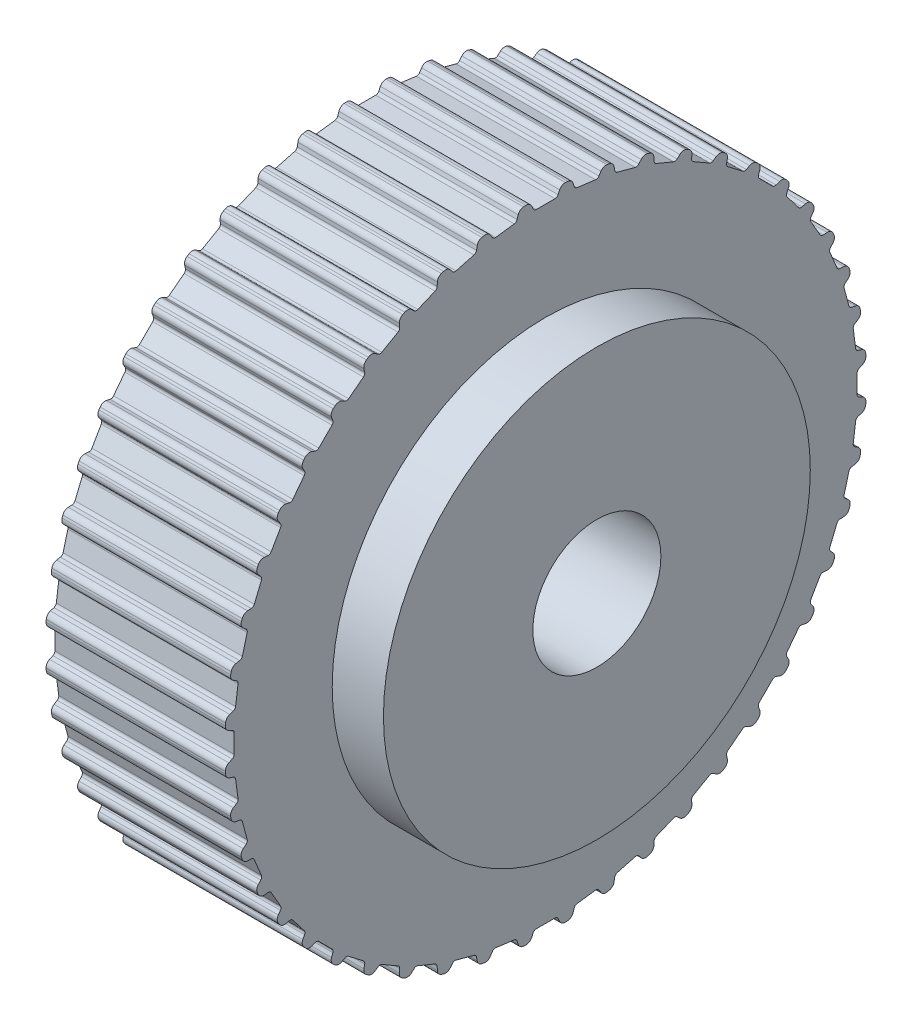
SolidWorks part; units mm, degrees
ref_plane "Front Plane" through (0, 0, 0) normal (0, 0, 1) x (1, 0, 0)
ref_plane "Top Plane" through (0, 0, 0) normal (0, 1, 0) x (1, 0, 0)
ref_plane "Right Plane" through (0, 0, 0) normal (1, 0, 0) x (0, 0, -1)
ref_plane "Plane1" through (0, 0, 0) normal (0, 0, -1) x (-1, 0, 0)
sketch "Sketch1" plane through (0, 0, 0) normal (0, 0, -1) x (-1, 0, 0)
  line L0 (-21, 37.585) -> (-21, 0)
  line L1 (-21, 0) -> (0, 0)
  line L2 (0, 0) -> (0, 37.585)
  line L3 (0, 37.585) -> (-21, 37.585)
  line L4 (-21, 0) -> (0, 0) construction
revolve "Revolve1" add sketch "Sketch1" angle 360 about L4
sketch "Sketch2" plane through (0, 0, 0) normal (-1, 0, 0) x (0, 0, 1)
  line L0 (3.0738, 37.4591) -> (3.4238, 36.3491)
  line L1 (3.4238, 36.3491) -> (6.1007, 35.9967)
  line L2 (6.1007, 35.9967) -> (6.7261, 36.9783)
  arc A0 (6.7261, 36.9783) -> (3.0738, 37.4591) centre (0, 0) ccw
extrude "Cut-Extrude1" cut sketch "Sketch2" against normal through all
sketch "Sketch3" plane through (0, 0, 0) normal (-1, 0, 0) x (0, 0, 1)
  line L0 (7.9369, 36.7374) -> (8.139, 35.5912)
  line L1 (8.139, 35.5912) -> (10.747, 34.8924)
  line L2 (10.747, 34.8924) -> (11.4951, 35.784)
  arc A0 (11.4951, 35.784) -> (7.9369, 36.7374) centre (0, 0) ccw
extrude "Cut-Extrude2" cut sketch "Sketch3" against normal through all
sketch "Sketch4" plane through (0, 0, 0) normal (-1, 0, 0) x (0, 0, 1)
  line L0 (12.6642, 35.3871) -> (12.715, 34.2244)
  line L1 (12.715, 34.2244) -> (15.2094, 33.1911)
  line L2 (15.2094, 33.1911) -> (16.0676, 33.9774)
  arc A0 (16.0676, 33.9774) -> (12.6642, 35.3871) centre (0, 0) ccw
extrude "Cut-Extrude3" cut sketch "Sketch4" against normal through all
sketch "Sketch5" plane through (0, 0, 0) normal (-1, 0, 0) x (0, 0, 1)
  line L0 (17.1748, 33.4314) -> (17.0734, 32.2719)
  line L1 (17.0734, 32.2719) -> (19.4116, 30.9219)
  line L2 (19.4116, 30.9219) -> (20.365, 31.5895)
  arc A0 (20.365, 31.5895) -> (17.1748, 33.4314) centre (0, 0) ccw
extrude "Cut-Extrude4" cut sketch "Sketch5" against normal through all
sketch "Sketch6" plane through (0, 0, 0) normal (-1, 0, 0) x (0, 0, 1)
  line L0 (21.3915, 30.9036) -> (21.1396, 29.7673)
  line L1 (21.1396, 29.7673) -> (23.2817, 28.1237)
  line L2 (23.2817, 28.1237) -> (24.3141, 28.6611)
  arc A0 (24.3141, 28.6611) -> (21.3915, 30.9036) centre (0, 0) ccw
extrude "Cut-Extrude5" cut sketch "Sketch6" against normal through all
sketch "Sketch7" plane through (0, 0, 0) normal (-1, 0, 0) x (0, 0, 1)
  line L0 (25.2423, 27.8471) -> (24.8442, 26.7534)
  line L1 (24.8442, 26.7534) -> (26.7534, 24.8442)
  line L2 (26.7534, 24.8442) -> (27.8471, 25.2423)
  arc A0 (27.8471, 25.2423) -> (25.2423, 27.8471) centre (0, 0) ccw
extrude "Cut-Extrude6" cut sketch "Sketch7" against normal through all
sketch "Sketch8" plane through (0, 0, 0) normal (-1, 0, 0) x (0, 0, 1)
  line L0 (28.6611, 24.3141) -> (28.1237, 23.2817)
  line L1 (28.1237, 23.2817) -> (29.7673, 21.1396)
  line L2 (29.7673, 21.1396) -> (30.9036, 21.3915)
  arc A0 (30.9036, 21.3915) -> (28.6611, 24.3141) centre (0, 0) ccw
extrude "Cut-Extrude7" cut sketch "Sketch8" against normal through all
sketch "Sketch9" plane through (0, 0, 0) normal (-1, 0, 0) x (0, 0, 1)
  line L0 (31.5895, 20.365) -> (30.9219, 19.4116)
  line L1 (30.9219, 19.4116) -> (32.2719, 17.0734)
  line L2 (32.2719, 17.0734) -> (33.4314, 17.1748)
  arc A0 (33.4314, 17.1748) -> (31.5895, 20.365) centre (0, 0) ccw
extrude "Cut-Extrude8" cut sketch "Sketch9" against normal through all
sketch "Sketch10" plane through (0, 0, 0) normal (-1, 0, 0) x (0, 0, 1)
  line L0 (33.9774, 16.0676) -> (33.1911, 15.2094)
  line L1 (33.1911, 15.2094) -> (34.2244, 12.715)
  line L2 (34.2244, 12.715) -> (35.3871, 12.6642)
  arc A0 (35.3871, 12.6642) -> (33.9774, 16.0676) centre (0, 0) ccw
extrude "Cut-Extrude9" cut sketch "Sketch10" against normal through all
sketch "Sketch11" plane through (0, 0, 0) normal (-1, 0, 0) x (0, 0, 1)
  line L0 (35.784, 11.4951) -> (34.8924, 10.747)
  line L1 (34.8924, 10.747) -> (35.5912, 8.139)
  line L2 (35.5912, 8.139) -> (36.7374, 7.9369)
  arc A0 (36.7374, 7.9369) -> (35.784, 11.4951) centre (0, 0) ccw
extrude "Cut-Extrude10" cut sketch "Sketch11" against normal through all
sketch "Sketch12" plane through (0, 0, 0) normal (-1, 0, 0) x (0, 0, 1)
  line L0 (36.9783, 6.7261) -> (35.9967, 6.1007)
  line L1 (35.9967, 6.1007) -> (36.3491, 3.4238)
  line L2 (36.3491, 3.4238) -> (37.4591, 3.0738)
  arc A0 (37.4591, 3.0738) -> (36.9783, 6.7261) centre (0, 0) ccw
extrude "Cut-Extrude11" cut sketch "Sketch12" against normal through all
sketch "Sketch13" plane through (0, 0, 0) normal (-1, 0, 0) x (0, 0, 1)
  line L0 (37.5398, 1.8419) -> (36.485, 1.35)
  line L1 (36.485, 1.35) -> (36.485, -1.35)
  line L2 (36.485, -1.35) -> (37.5398, -1.8419)
  arc A0 (37.5398, -1.8419) -> (37.5398, 1.8419) centre (0, 0) ccw
extrude "Cut-Extrude12" cut sketch "Sketch13" against normal through all
sketch "Sketch14" plane through (0, 0, 0) normal (-1, 0, 0) x (0, 0, 1)
  line L0 (37.4591, -3.0738) -> (36.3491, -3.4238)
  line L1 (36.3491, -3.4238) -> (35.9967, -6.1007)
  line L2 (35.9967, -6.1007) -> (36.9783, -6.7261)
  arc A0 (36.9783, -6.7261) -> (37.4591, -3.0738) centre (0, 0) ccw
extrude "Cut-Extrude13" cut sketch "Sketch14" against normal through all
sketch "Sketch15" plane through (0, 0, 0) normal (-1, 0, 0) x (0, 0, 1)
  line L0 (36.7374, -7.9369) -> (35.5912, -8.139)
  line L1 (35.5912, -8.139) -> (34.8924, -10.747)
  line L2 (34.8924, -10.747) -> (35.784, -11.4951)
  arc A0 (35.784, -11.4951) -> (36.7374, -7.9369) centre (0, 0) ccw
extrude "Cut-Extrude14" cut sketch "Sketch15" against normal through all
sketch "Sketch16" plane through (0, 0, 0) normal (-1, 0, 0) x (0, 0, 1)
  line L0 (35.3871, -12.6642) -> (34.2244, -12.715)
  line L1 (34.2244, -12.715) -> (33.1911, -15.2094)
  line L2 (33.1911, -15.2094) -> (33.9774, -16.0676)
  arc A0 (33.9774, -16.0676) -> (35.3871, -12.6642) centre (0, 0) ccw
extrude "Cut-Extrude15" cut sketch "Sketch16" against normal through all
sketch "Sketch17" plane through (0, 0, 0) normal (-1, 0, 0) x (0, 0, 1)
  line L0 (33.4314, -17.1748) -> (32.2719, -17.0734)
  line L1 (32.2719, -17.0734) -> (30.9219, -19.4116)
  line L2 (30.9219, -19.4116) -> (31.5895, -20.365)
  arc A0 (31.5895, -20.365) -> (33.4314, -17.1748) centre (0, 0) ccw
extrude "Cut-Extrude16" cut sketch "Sketch17" against normal through all
sketch "Sketch18" plane through (0, 0, 0) normal (-1, 0, 0) x (0, 0, 1)
  line L0 (30.9036, -21.3915) -> (29.7673, -21.1396)
  line L1 (29.7673, -21.1396) -> (28.1237, -23.2817)
  line L2 (28.1237, -23.2817) -> (28.6611, -24.3141)
  arc A0 (28.6611, -24.3141) -> (30.9036, -21.3915) centre (0, 0) ccw
extrude "Cut-Extrude17" cut sketch "Sketch18" against normal through all
sketch "Sketch19" plane through (0, 0, 0) normal (-1, 0, 0) x (0, 0, 1)
  line L0 (27.8471, -25.2423) -> (26.7534, -24.8442)
  line L1 (26.7534, -24.8442) -> (24.8442, -26.7534)
  line L2 (24.8442, -26.7534) -> (25.2423, -27.8471)
  arc A0 (25.2423, -27.8471) -> (27.8471, -25.2423) centre (0, 0) ccw
extrude "Cut-Extrude18" cut sketch "Sketch19" against normal through all
sketch "Sketch20" plane through (0, 0, 0) normal (-1, 0, 0) x (0, 0, 1)
  line L0 (24.3141, -28.6611) -> (23.2817, -28.1237)
  line L1 (23.2817, -28.1237) -> (21.1396, -29.7673)
  line L2 (21.1396, -29.7673) -> (21.3915, -30.9036)
  arc A0 (21.3915, -30.9036) -> (24.3141, -28.6611) centre (0, 0) ccw
extrude "Cut-Extrude19" cut sketch "Sketch20" against normal through all
sketch "Sketch21" plane through (0, 0, 0) normal (-1, 0, 0) x (0, 0, 1)
  line L0 (20.365, -31.5895) -> (19.4116, -30.9219)
  line L1 (19.4116, -30.9219) -> (17.0734, -32.2719)
  line L2 (17.0734, -32.2719) -> (17.1748, -33.4314)
  arc A0 (17.1748, -33.4314) -> (20.365, -31.5895) centre (0, 0) ccw
extrude "Cut-Extrude20" cut sketch "Sketch21" against normal through all
sketch "Sketch22" plane through (0, 0, 0) normal (-1, 0, 0) x (0, 0, 1)
  line L0 (16.0676, -33.9774) -> (15.2094, -33.1911)
  line L1 (15.2094, -33.1911) -> (12.715, -34.2244)
  line L2 (12.715, -34.2244) -> (12.6642, -35.3871)
  arc A0 (12.6642, -35.3871) -> (16.0676, -33.9774) centre (0, 0) ccw
extrude "Cut-Extrude21" cut sketch "Sketch22" against normal through all
sketch "Sketch23" plane through (0, 0, 0) normal (-1, 0, 0) x (0, 0, 1)
  line L0 (11.4951, -35.784) -> (10.747, -34.8924)
  line L1 (10.747, -34.8924) -> (8.139, -35.5912)
  line L2 (8.139, -35.5912) -> (7.9369, -36.7374)
  arc A0 (7.9369, -36.7374) -> (11.4951, -35.784) centre (0, 0) ccw
extrude "Cut-Extrude22" cut sketch "Sketch23" against normal through all
sketch "Sketch24" plane through (0, 0, 0) normal (-1, 0, 0) x (0, 0, 1)
  line L0 (6.7261, -36.9783) -> (6.1007, -35.9967)
  line L1 (6.1007, -35.9967) -> (3.4238, -36.3491)
  line L2 (3.4238, -36.3491) -> (3.0738, -37.4591)
  arc A0 (3.0738, -37.4591) -> (6.7261, -36.9783) centre (0, 0) ccw
extrude "Cut-Extrude23" cut sketch "Sketch24" against normal through all
sketch "Sketch25" plane through (0, 0, 0) normal (-1, 0, 0) x (0, 0, 1)
  line L0 (1.8419, -37.5398) -> (1.35, -36.485)
  line L1 (1.35, -36.485) -> (-1.35, -36.485)
  line L2 (-1.35, -36.485) -> (-1.8419, -37.5398)
  arc A0 (-1.8419, -37.5398) -> (1.8419, -37.5398) centre (0, 0) ccw
extrude "Cut-Extrude24" cut sketch "Sketch25" against normal through all
sketch "Sketch26" plane through (0, 0, 0) normal (-1, 0, 0) x (0, 0, 1)
  line L0 (-3.0738, -37.4591) -> (-3.4238, -36.3491)
  line L1 (-3.4238, -36.3491) -> (-6.1007, -35.9967)
  line L2 (-6.1007, -35.9967) -> (-6.7261, -36.9783)
  arc A0 (-6.7261, -36.9783) -> (-3.0738, -37.4591) centre (0, 0) ccw
extrude "Cut-Extrude25" cut sketch "Sketch26" against normal through all
sketch "Sketch27" plane through (0, 0, 0) normal (-1, 0, 0) x (0, 0, 1)
  line L0 (-7.9369, -36.7374) -> (-8.139, -35.5912)
  line L1 (-8.139, -35.5912) -> (-10.747, -34.8924)
  line L2 (-10.747, -34.8924) -> (-11.4951, -35.784)
  arc A0 (-11.4951, -35.784) -> (-7.9369, -36.7374) centre (0, 0) ccw
extrude "Cut-Extrude26" cut sketch "Sketch27" against normal through all
sketch "Sketch28" plane through (0, 0, 0) normal (-1, 0, 0) x (0, 0, 1)
  line L0 (-12.6642, -35.3871) -> (-12.715, -34.2244)
  line L1 (-12.715, -34.2244) -> (-15.2094, -33.1911)
  line L2 (-15.2094, -33.1911) -> (-16.0676, -33.9774)
  arc A0 (-16.0676, -33.9774) -> (-12.6642, -35.3871) centre (0, 0) ccw
extrude "Cut-Extrude27" cut sketch "Sketch28" against normal through all
sketch "Sketch29" plane through (0, 0, 0) normal (-1, 0, 0) x (0, 0, 1)
  line L0 (-17.1748, -33.4314) -> (-17.0734, -32.2719)
  line L1 (-17.0734, -32.2719) -> (-19.4116, -30.9219)
  line L2 (-19.4116, -30.9219) -> (-20.365, -31.5895)
  arc A0 (-20.365, -31.5895) -> (-17.1748, -33.4314) centre (0, 0) ccw
extrude "Cut-Extrude28" cut sketch "Sketch29" against normal through all
sketch "Sketch30" plane through (0, 0, 0) normal (-1, 0, 0) x (0, 0, 1)
  line L0 (-21.3915, -30.9036) -> (-21.1396, -29.7673)
  line L1 (-21.1396, -29.7673) -> (-23.2817, -28.1237)
  line L2 (-23.2817, -28.1237) -> (-24.3141, -28.6611)
  arc A0 (-24.3141, -28.6611) -> (-21.3915, -30.9036) centre (0, 0) ccw
extrude "Cut-Extrude29" cut sketch "Sketch30" against normal through all
sketch "Sketch31" plane through (0, 0, 0) normal (-1, 0, 0) x (0, 0, 1)
  line L0 (-25.2423, -27.8471) -> (-24.8442, -26.7534)
  line L1 (-24.8442, -26.7534) -> (-26.7534, -24.8442)
  line L2 (-26.7534, -24.8442) -> (-27.8471, -25.2423)
  arc A0 (-27.8471, -25.2423) -> (-25.2423, -27.8471) centre (0, 0) ccw
extrude "Cut-Extrude30" cut sketch "Sketch31" against normal through all
sketch "Sketch32" plane through (0, 0, 0) normal (-1, 0, 0) x (0, 0, 1)
  line L0 (-28.6611, -24.3141) -> (-28.1237, -23.2817)
  line L1 (-28.1237, -23.2817) -> (-29.7673, -21.1396)
  line L2 (-29.7673, -21.1396) -> (-30.9036, -21.3915)
  arc A0 (-30.9036, -21.3915) -> (-28.6611, -24.3141) centre (0, 0) ccw
extrude "Cut-Extrude31" cut sketch "Sketch32" against normal through all
sketch "Sketch33" plane through (0, 0, 0) normal (-1, 0, 0) x (0, 0, 1)
  line L0 (-31.5895, -20.365) -> (-30.9219, -19.4116)
  line L1 (-30.9219, -19.4116) -> (-32.2719, -17.0734)
  line L2 (-32.2719, -17.0734) -> (-33.4314, -17.1748)
  arc A0 (-33.4314, -17.1748) -> (-31.5895, -20.365) centre (0, 0) ccw
extrude "Cut-Extrude32" cut sketch "Sketch33" against normal through all
sketch "Sketch34" plane through (0, 0, 0) normal (-1, 0, 0) x (0, 0, 1)
  line L0 (-33.9774, -16.0676) -> (-33.1911, -15.2094)
  line L1 (-33.1911, -15.2094) -> (-34.2244, -12.715)
  line L2 (-34.2244, -12.715) -> (-35.3871, -12.6642)
  arc A0 (-35.3871, -12.6642) -> (-33.9774, -16.0676) centre (0, 0) ccw
extrude "Cut-Extrude33" cut sketch "Sketch34" against normal through all
sketch "Sketch35" plane through (0, 0, 0) normal (-1, 0, 0) x (0, 0, 1)
  line L0 (-35.784, -11.4951) -> (-34.8924, -10.747)
  line L1 (-34.8924, -10.747) -> (-35.5912, -8.139)
  line L2 (-35.5912, -8.139) -> (-36.7374, -7.9369)
  arc A0 (-36.7374, -7.9369) -> (-35.784, -11.4951) centre (0, 0) ccw
extrude "Cut-Extrude34" cut sketch "Sketch35" against normal through all
sketch "Sketch36" plane through (0, 0, 0) normal (-1, 0, 0) x (0, 0, 1)
  line L0 (-36.9783, -6.7261) -> (-35.9967, -6.1007)
  line L1 (-35.9967, -6.1007) -> (-36.3491, -3.4238)
  line L2 (-36.3491, -3.4238) -> (-37.4591, -3.0738)
  arc A0 (-37.4591, -3.0738) -> (-36.9783, -6.7261) centre (0, 0) ccw
extrude "Cut-Extrude35" cut sketch "Sketch36" against normal through all
sketch "Sketch37" plane through (0, 0, 0) normal (-1, 0, 0) x (0, 0, 1)
  line L0 (-37.5398, -1.8419) -> (-36.485, -1.35)
  line L1 (-36.485, -1.35) -> (-36.485, 1.35)
  line L2 (-36.485, 1.35) -> (-37.5398, 1.8419)
  arc A0 (-37.5398, 1.8419) -> (-37.5398, -1.8419) centre (0, 0) ccw
extrude "Cut-Extrude36" cut sketch "Sketch37" against normal through all
sketch "Sketch38" plane through (0, 0, 0) normal (-1, 0, 0) x (0, 0, 1)
  line L0 (-37.4591, 3.0738) -> (-36.3491, 3.4238)
  line L1 (-36.3491, 3.4238) -> (-35.9967, 6.1007)
  line L2 (-35.9967, 6.1007) -> (-36.9783, 6.7261)
  arc A0 (-36.9783, 6.7261) -> (-37.4591, 3.0738) centre (0, 0) ccw
extrude "Cut-Extrude37" cut sketch "Sketch38" against normal through all
sketch "Sketch39" plane through (0, 0, 0) normal (-1, 0, 0) x (0, 0, 1)
  line L0 (-36.7374, 7.9369) -> (-35.5912, 8.139)
  line L1 (-35.5912, 8.139) -> (-34.8924, 10.747)
  line L2 (-34.8924, 10.747) -> (-35.784, 11.4951)
  arc A0 (-35.784, 11.4951) -> (-36.7374, 7.9369) centre (0, 0) ccw
extrude "Cut-Extrude38" cut sketch "Sketch39" against normal through all
sketch "Sketch40" plane through (0, 0, 0) normal (-1, 0, 0) x (0, 0, 1)
  line L0 (-35.3871, 12.6642) -> (-34.2244, 12.715)
  line L1 (-34.2244, 12.715) -> (-33.1911, 15.2094)
  line L2 (-33.1911, 15.2094) -> (-33.9774, 16.0676)
  arc A0 (-33.9774, 16.0676) -> (-35.3871, 12.6642) centre (0, 0) ccw
extrude "Cut-Extrude39" cut sketch "Sketch40" against normal through all
sketch "Sketch41" plane through (0, 0, 0) normal (-1, 0, 0) x (0, 0, 1)
  line L0 (-33.4314, 17.1748) -> (-32.2719, 17.0734)
  line L1 (-32.2719, 17.0734) -> (-30.9219, 19.4116)
  line L2 (-30.9219, 19.4116) -> (-31.5895, 20.365)
  arc A0 (-31.5895, 20.365) -> (-33.4314, 17.1748) centre (0, 0) ccw
extrude "Cut-Extrude40" cut sketch "Sketch41" against normal through all
sketch "Sketch42" plane through (0, 0, 0) normal (-1, 0, 0) x (0, 0, 1)
  line L0 (-30.9036, 21.3915) -> (-29.7673, 21.1396)
  line L1 (-29.7673, 21.1396) -> (-28.1237, 23.2817)
  line L2 (-28.1237, 23.2817) -> (-28.6611, 24.3141)
  arc A0 (-28.6611, 24.3141) -> (-30.9036, 21.3915) centre (0, 0) ccw
extrude "Cut-Extrude41" cut sketch "Sketch42" against normal through all
sketch "Sketch43" plane through (0, 0, 0) normal (-1, 0, 0) x (0, 0, 1)
  line L0 (-27.8471, 25.2423) -> (-26.7534, 24.8442)
  line L1 (-26.7534, 24.8442) -> (-24.8442, 26.7534)
  line L2 (-24.8442, 26.7534) -> (-25.2423, 27.8471)
  arc A0 (-25.2423, 27.8471) -> (-27.8471, 25.2423) centre (0, 0) ccw
extrude "Cut-Extrude42" cut sketch "Sketch43" against normal through all
sketch "Sketch44" plane through (0, 0, 0) normal (-1, 0, 0) x (0, 0, 1)
  line L0 (-24.3141, 28.6611) -> (-23.2817, 28.1237)
  line L1 (-23.2817, 28.1237) -> (-21.1396, 29.7673)
  line L2 (-21.1396, 29.7673) -> (-21.3915, 30.9036)
  arc A0 (-21.3915, 30.9036) -> (-24.3141, 28.6611) centre (0, 0) ccw
extrude "Cut-Extrude43" cut sketch "Sketch44" against normal through all
sketch "Sketch45" plane through (0, 0, 0) normal (-1, 0, 0) x (0, 0, 1)
  line L0 (-20.365, 31.5895) -> (-19.4116, 30.9219)
  line L1 (-19.4116, 30.9219) -> (-17.0734, 32.2719)
  line L2 (-17.0734, 32.2719) -> (-17.1748, 33.4314)
  arc A0 (-17.1748, 33.4314) -> (-20.365, 31.5895) centre (0, 0) ccw
extrude "Cut-Extrude44" cut sketch "Sketch45" against normal through all
sketch "Sketch46" plane through (0, 0, 0) normal (-1, 0, 0) x (0, 0, 1)
  line L0 (-16.0676, 33.9774) -> (-15.2094, 33.1911)
  line L1 (-15.2094, 33.1911) -> (-12.715, 34.2244)
  line L2 (-12.715, 34.2244) -> (-12.6642, 35.3871)
  arc A0 (-12.6642, 35.3871) -> (-16.0676, 33.9774) centre (0, 0) ccw
extrude "Cut-Extrude45" cut sketch "Sketch46" against normal through all
sketch "Sketch47" plane through (0, 0, 0) normal (-1, 0, 0) x (0, 0, 1)
  line L0 (-11.4951, 35.784) -> (-10.747, 34.8924)
  line L1 (-10.747, 34.8924) -> (-8.139, 35.5912)
  line L2 (-8.139, 35.5912) -> (-7.9369, 36.7374)
  arc A0 (-7.9369, 36.7374) -> (-11.4951, 35.784) centre (0, 0) ccw
extrude "Cut-Extrude46" cut sketch "Sketch47" against normal through all
sketch "Sketch48" plane through (0, 0, 0) normal (-1, 0, 0) x (0, 0, 1)
  line L0 (-6.7261, 36.9783) -> (-6.1007, 35.9967)
  line L1 (-6.1007, 35.9967) -> (-3.4238, 36.3491)
  line L2 (-3.4238, 36.3491) -> (-3.0738, 37.4591)
  arc A0 (-3.0738, 37.4591) -> (-6.7261, 36.9783) centre (0, 0) ccw
extrude "Cut-Extrude47" cut sketch "Sketch48" against normal through all
sketch "Sketch49" plane through (0, 0, 0) normal (-1, 0, 0) x (0, 0, 1)
  line L0 (-1.8419, 37.5398) -> (-1.35, 36.485)
  line L1 (-1.35, 36.485) -> (1.35, 36.485)
  line L2 (1.35, 36.485) -> (1.8419, 37.5398)
  arc A0 (1.8419, 37.5398) -> (-1.8419, 37.5398) centre (0, 0) ccw
extrude "Cut-Extrude48" cut sketch "Sketch49" against normal through all
sketch "Sketch50" plane through (0, 0, 0) normal (0, 0, -1) x (-1, 0, 0)
  line L0 (-27, 25) -> (-27, 0)
  line L1 (-27, 0) -> (-21, 0)
  line L2 (-21, 0) -> (-21, 25)
  line L3 (-21, 25) -> (-27, 25)
  line L4 (-27, 0) -> (-21, 0) construction
revolve "Revolve2" add sketch "Sketch50" angle 360 about L4
hole_wizard "Ø8.0 (8) Diameter Hole1" positions "Sketch52" profile "Sketch51" hole size "Ø8.0" standard "ANSI Metric"
sketch "Sketch52" plane through (27, 0, 0) normal (1, 0, 0) x (0, 0, -1)
  point P0 (0, 0)
sketch "Sketch51" plane through (27, 0, 0) normal (0, 1, 0) x (0, 0, -1)
  line L0 (0, 0) -> (0, 27)
  line L1 (0, 27) -> (4, 27)
  line L2 (4, 27) -> (4, 0)
  line L5 (4, 0) -> (0, 0)
  line L11 (0, -6.35) -> (0, 107.95) construction
  dimension "Thru Hole Dia." = 8
  dimension "Thru Hole Depth" = 27
fillet "Fillet1" radius 0.4 96 edges at (10.5, -19.4116, -30.9219) (10.5, 36.485, -1.35) (10.5, 17.0734, -32.2719) (10.5, 36.3491, 3.4238) (10.5, -32.2719, -17.0734) (10.5, 34.8924, 10.747) (10.5, -1.35, -36.485) (10.5, 35.5912, 8.139) (10.5, 30.9219, -19.4116) (10.5, 33.1911, 15.2094) (10.5, -35.5912, -8.139) (10.5, 34.2244, 12.715) (10.5, -26.7534, -24.8442) (10.5, 30.9219, 19.4116) (10.5, -10.747, -34.8924) (10.5, 32.2719, 17.0734) (10.5, 8.139, -35.5912) (10.5, 28.1237, 23.2817) (10.5, 24.8442, -26.7534) (10.5, 29.7673, 21.1396) (10.5, 34.8924, -10.747) (10.5, 24.8442, 26.7534) (10.5, -36.3491, -3.4238) (10.5, 26.7534, 24.8442) (10.5, -34.2244, -12.715) (10.5, 21.1396, 29.7673) (10.5, -29.7673, -21.1396) (10.5, 23.2817, 28.1237) (10.5, -23.2817, -28.1237) (10.5, 17.0734, 32.2719) (10.5, -15.2094, -33.1911) (10.5, 19.4116, 30.9219) (10.5, -6.1007, -35.9967) (10.5, 12.715, 34.2244) (10.5, 3.4238, -36.3491) (10.5, 15.2094, 33.1911) (10.5, 12.715, -34.2244) (10.5, 8.139, 35.5912) (10.5, 21.1396, -29.7673) (10.5, 10.747, 34.8924) (10.5, 28.1237, -23.2817) (10.5, 3.4238, 36.3491) (10.5, 33.1911, -15.2094) (10.5, 6.1007, 35.9967) (10.5, 35.9967, -6.1007) (10.5, -1.35, 36.485) (10.5, -35.9967, -6.1007) (10.5, 1.35, 36.485) (10.5, -34.8924, -10.747) (10.5, -6.1007, 35.9967) (10.5, -33.1911, -15.2094) (10.5, -3.4238, 36.3491) (10.5, -30.9219, -19.4116) (10.5, -10.747, 34.8924) (10.5, -28.1237, -23.2817) (10.5, -8.139, 35.5912) (10.5, -24.8442, -26.7534) (10.5, -15.2094, 33.1911) (10.5, -21.1396, -29.7673) (10.5, -12.715, 34.2244) (10.5, -17.0734, -32.2719) (10.5, -19.4116, 30.9219) (10.5, -12.715, -34.2244) (10.5, -17.0734, 32.2719) (10.5, -8.139, -35.5912) (10.5, -23.2817, 28.1237) (10.5, -3.4238, -36.3491) (10.5, -21.1396, 29.7673) (10.5, 1.35, -36.485) (10.5, -26.7534, 24.8442) (10.5, 6.1007, -35.9967) (10.5, -24.8442, 26.7534) (10.5, 10.747, -34.8924) (10.5, -29.7673, 21.1396) (10.5, 15.2094, -33.1911) (10.5, -28.1237, 23.2817) (10.5, 19.4116, -30.9219) (10.5, -32.2719, 17.0734) (10.5, 23.2817, -28.1237) (10.5, -30.9219, 19.4116) (10.5, 26.7534, -24.8442) (10.5, -34.2244, 12.715) (10.5, 29.7673, -21.1396) (10.5, -33.1911, 15.2094) (10.5, 32.2719, -17.0734) (10.5, -35.5912, 8.139) (10.5, 34.2244, -12.715) (10.5, -34.8924, 10.747) (10.5, 35.5912, -8.139) (10.5, -36.3491, 3.4238) (10.5, 36.3491, -3.4238) (10.5, -35.9967, 6.1007) (10.5, 36.485, 1.35) (10.5, -36.485, -1.35) (10.5, 35.9967, 6.1007) (10.5, -36.485, 1.35)
fillet "Fillet2" radius 0.7 96 edges at (10.5, -20.365, -31.5895) (10.5, 36.9783, 6.7261) (10.5, 17.1748, -33.4314) (10.5, 37.4591, 3.0738) (10.5, -33.4314, -17.1748) (10.5, 35.784, 11.4951) (10.5, -1.8419, -37.5398) (10.5, 36.7374, 7.9369) (10.5, 31.5895, -20.365) (10.5, 33.9774, 16.0676) (10.5, -36.7374, -7.9369) (10.5, 35.3871, 12.6642) (10.5, -27.8471, -25.2423) (10.5, 31.5895, 20.365) (10.5, -11.4951, -35.784) (10.5, 33.4314, 17.1748) (10.5, 7.9369, -36.7374) (10.5, 28.6611, 24.3141) (10.5, 25.2423, -27.8471) (10.5, 30.9036, 21.3915) (10.5, 35.784, -11.4951) (10.5, 25.2423, 27.8471) (10.5, -37.4591, -3.0738) (10.5, 27.8471, 25.2423) (10.5, -35.3871, -12.6642) (10.5, 21.3915, 30.9036) (10.5, -30.9036, -21.3915) (10.5, 24.3141, 28.6611) (10.5, -24.3141, -28.6611) (10.5, 17.1748, 33.4314) (10.5, -16.0676, -33.9774) (10.5, 20.365, 31.5895) (10.5, -6.7261, -36.9783) (10.5, 12.6642, 35.3871) (10.5, 3.0738, -37.4591) (10.5, 16.0676, 33.9774) (10.5, 12.6642, -35.3871) (10.5, 7.9369, 36.7374) (10.5, 21.3915, -30.9036) (10.5, 11.4951, 35.784) (10.5, 28.6611, -24.3141) (10.5, 3.0738, 37.4591) (10.5, 33.9774, -16.0676) (10.5, 6.7261, 36.9783) (10.5, 36.9783, -6.7261) (10.5, -1.8419, 37.5398) (10.5, -36.9783, -6.7261) (10.5, 1.8419, 37.5398) (10.5, -35.784, -11.4951) (10.5, -6.7261, 36.9783) (10.5, -33.9774, -16.0676) (10.5, -3.0738, 37.4591) (10.5, -31.5895, -20.365) (10.5, -11.4951, 35.784) (10.5, -28.6611, -24.3141) (10.5, -7.9369, 36.7374) (10.5, -25.2423, -27.8471) (10.5, -16.0676, 33.9774) (10.5, -21.3915, -30.9036) (10.5, -12.6642, 35.3871) (10.5, -17.1748, -33.4314) (10.5, -20.365, 31.5895) (10.5, -12.6642, -35.3871) (10.5, -17.1748, 33.4314) (10.5, -7.9369, -36.7374) (10.5, -24.3141, 28.6611) (10.5, -3.0738, -37.4591) (10.5, -21.3915, 30.9036) (10.5, 1.8419, -37.5398) (10.5, -27.8471, 25.2423) (10.5, 6.7261, -36.9783) (10.5, -25.2423, 27.8471) (10.5, 11.4951, -35.784) (10.5, -30.9036, 21.3915) (10.5, 16.0676, -33.9774) (10.5, -28.6611, 24.3141) (10.5, 20.365, -31.5895) (10.5, -33.4314, 17.1748) (10.5, 24.3141, -28.6611) (10.5, -31.5895, 20.365) (10.5, 27.8471, -25.2423) (10.5, -35.3871, 12.6642) (10.5, 30.9036, -21.3915) (10.5, -33.9774, 16.0676) (10.5, 33.4314, -17.1748) (10.5, -36.7374, 7.9369) (10.5, 35.3871, -12.6642) (10.5, -35.784, 11.4951) (10.5, 36.7374, -7.9369) (10.5, -37.4591, 3.0738) (10.5, 37.4591, -3.0738) (10.5, -36.9783, 6.7261) (10.5, 37.5398, 1.8419) (10.5, -37.5398, -1.8419) (10.5, -37.5398, 1.8419) (10.5, 37.5398, -1.8419)
sketch "Sketch53" plane through (27, 0, 0) normal (1, 0, 0) x (0, 0, -1)
  circle A0 centre (0, 0) radius 7.5
  dimension "D1" = 15
extrude "Cut-Extrude49" cut sketch "Sketch53" against normal through all
